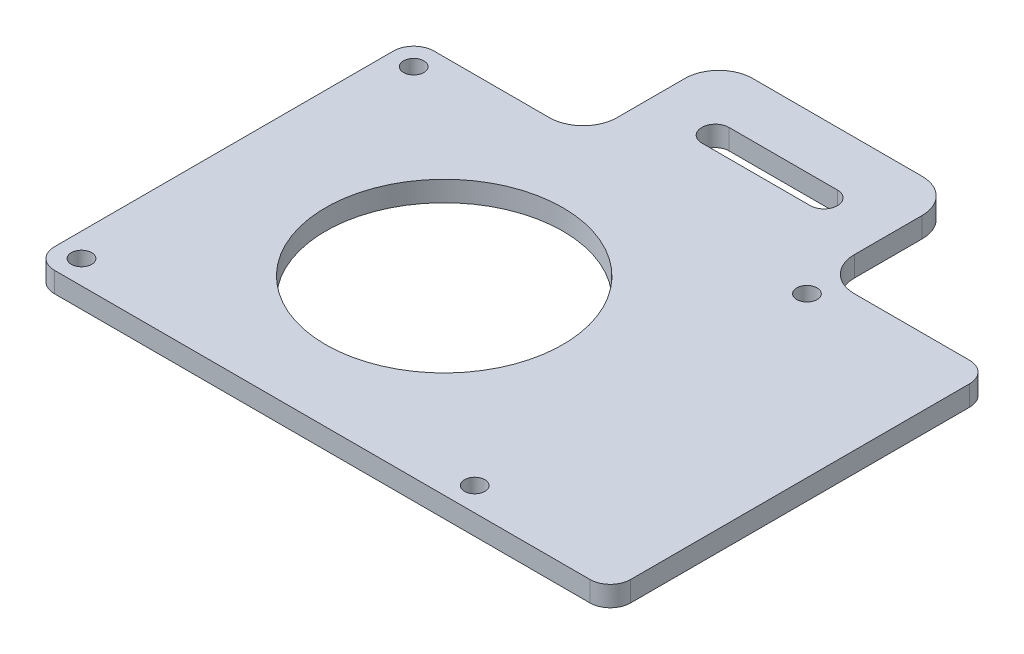
SolidWorks part; units mm, degrees
ref_plane "前视基准面" through (0, 0, 0) normal (0, 0, 1) x (1, 0, 0)
ref_plane "上视基准面" through (0, 0, 0) normal (0, 1, 0) x (1, 0, 0)
ref_plane "右视基准面" through (0, 0, 0) normal (1, 0, 0) x (0, 0, -1)
sketch "Sketch1" plane through (0, 0, 0) normal (0, 1, 0) x (1, 0, 0)
  line L1 (-42.5, -28) -> (42.5, -28)
  line L2 (-42.5, -28) -> (-42.5, 28)
  line L3 (-42.5, 28) -> (42.5, 28)
  line L4 (42.5, -28) -> (42.5, 28)
  line L5 (-42.5, -28) -> (42.5, 28) construction
  line L6 (-42.5, 28) -> (42.5, -28) construction
  point P0 (0, 0)
  dimension "D1" = 85
  dimension "D2" = 56
extrude "Boss-Extrude1" add sketch "Sketch1" along normal blind 3
sketch "Sketch2" plane through (0, 3, 0) normal (0, 1, 0) x (1, 0, 0)
  line L0 (-42.5, 28) -> (-42.5, -28) construction
  line L1 (-39, -24.5) -> (19, -24.5) construction
  line L2 (-39, -24.5) -> (-39, 24.5) construction
  line L3 (-39, 24.5) -> (19, 24.5) construction
  line L4 (19, -24.5) -> (19, 24.5) construction
  line L5 (-39, -24.5) -> (19, 24.5) construction
  line L6 (-39, 24.5) -> (19, -24.5) construction
  circle A0 centre (-39, 24.5) radius 1.5
  circle A1 centre (19, 24.5) radius 1.5
  circle A2 centre (19, -24.5) radius 1.5
  circle A3 centre (-39, -24.5) radius 1.5
  point P0 (-10, 0)
  point P9 (-5.6325, 0)
  point P12 (0, 0)
  dimension "D1" = 3
  dimension "D2" = 58
  dimension "D3" = 49
  dimension "D4" = 3.5
extrude "Cut-Extrude1" cut sketch "Sketch2" against normal through all both and the other way through all
fillet "Fillet1" radius 3 4 edges at (42.5, 1.5, 28) (42.5, 1.5, -28) (-42.5, 1.5, 28) (-42.5, 1.5, -28)
sketch "Sketch3" plane through (0, 3, 0) normal (0, 1, 0) x (1, 0, 0)
  line L0 (-39, 24.5) -> (19, -24.5) construction
  circle A0 centre (-10, 0) radius 17.5
  dimension "D1" = 35
extrude "Cut-Extrude2" cut sketch "Sketch3" against normal through all both and the other way through all
sketch "Sketch4" plane through (0, 3, 0) normal (0, 1, 0) x (1, 0, 0)
  line L0 (-17.5, 28) -> (17.5, 28)
  line L1 (-17.5, 28) -> (-17.5, 48)
  line L2 (17.5, 28) -> (17.5, 48)
  line L3 (-17.5, 48) -> (17.5, 48)
  line L4 (39.5, 28) -> (-39.5, 28) construction
  line L5 (0, 0) -> (0, 28) construction
  dimension "D1" = 35
  dimension "D2" = 20
extrude "Boss-Extrude2" add sketch "Sketch4" against normal up to surface (3 mm away) contours L0 L1 L3 L2 up to face at (-10, 0, 17.5)
fillet "Fillet2" radius 5 4 edges at (17.5, 1.5, -28) (17.5, 1.5, -48) (-17.5, 1.5, -48) (-17.5, 1.5, -28)
sketch "Sketch5" plane through (0, 3, 0) normal (0, 1, 0) x (1, 0, 0)
  line L0 (-17.5, 38) -> (17.5, 38) construction
  line L1 (-17.5, 33) -> (-17.5, 43) construction
  line L2 (17.5, 33) -> (17.5, 43) construction
  line L3 (-8, 38) -> (8, 38) construction
  line L4 (-8, 40) -> (8, 40)
  line L5 (-8, 36) -> (8, 36)
  arc A0 (-8, 40) -> (-8, 36) centre (-8, 38) ccw
  arc A1 (8, 36) -> (8, 40) centre (8, 38) ccw
  point P8 (0, 38)
  dimension "D1" = 4
  dimension "D2" = 16
extrude "Cut-Extrude3" cut sketch "Sketch5" against normal through all both and the other way through all
